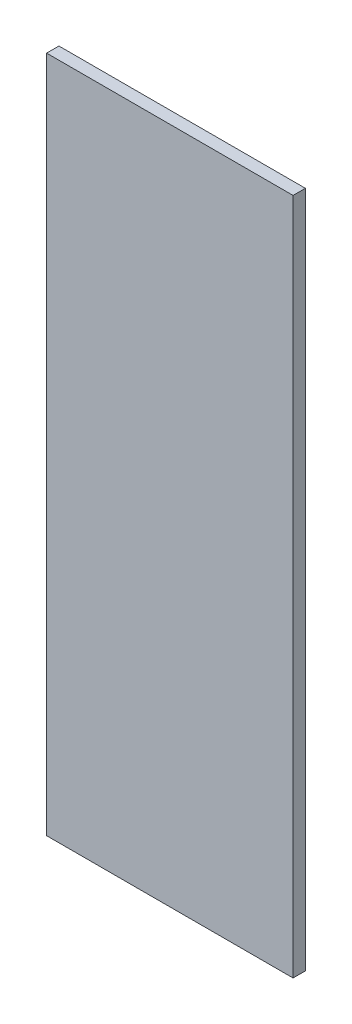
SolidWorks part; units mm, degrees
ref_plane "前视基准面" through (0, 0, 0) normal (0, 0, 1) x (1, 0, 0)
ref_plane "上视基准面" through (0, 0, 0) normal (0, 1, 0) x (1, 0, 0)
ref_plane "右视基准面" through (0, 0, 0) normal (1, 0, 0) x (0, 0, -1)
sketch "草图1" plane through (0, 0, 0) normal (0, 0, 1) x (1, 0, 0)
  line L1 (-50, -137.5) -> (50, -137.5)
  line L2 (-50, -137.5) -> (-50, 137.5)
  line L3 (-50, 137.5) -> (50, 137.5)
  line L4 (50, -137.5) -> (50, 137.5)
  line L5 (-50, -137.5) -> (50, 137.5) construction
  line L6 (-50, 137.5) -> (50, -137.5) construction
  point P0 (0, 0)
  dimension "D1" = 100
  dimension "D2" = 275
extrude "凸台-拉伸1" add sketch "草图1" along normal blind 5
